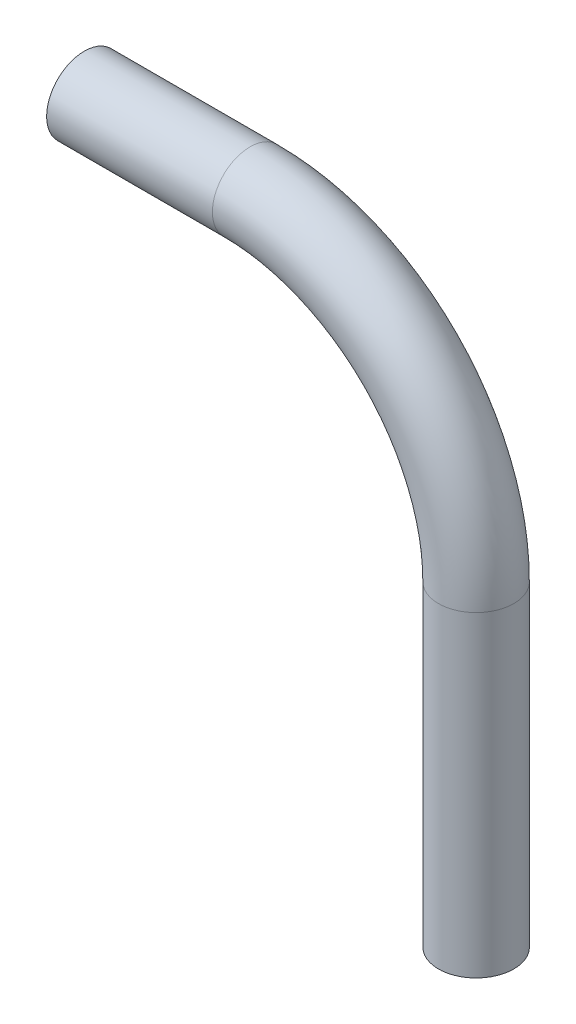
SolidWorks part; units mm, degrees
material "6061-T6 (SS)"
ref_plane "Front Plane" through (0, 0, 0) normal (0, 0, 1) x (1, 0, 0)
ref_plane "Top Plane" through (0, 0, 0) normal (0, 1, 0) x (1, 0, 0)
ref_plane "Right Plane" through (0, 0, 0) normal (1, 0, 0) x (0, 0, -1)
sketch "Sketch1" plane through (0, 0, 0) normal (0, 0, 1) x (1, 0, 0)
  line L0 (35.3114, 20.9627) -> (49.2814, 20.9627)
  line L1 (68.3314, 1.9127) -> (68.3314, -24.7573)
  line L2 (68.3314, -24.7573) -> (68.3314, 23.4845)
  line L3 (35.3114, 20.9627) -> (71.7681, 20.9627)
  arc A0 (49.2814, 20.9627) -> (68.3314, 1.9127) centre (49.2814, 1.9127) cw
  point P4 (68.3314, 20.9627)
  point P8 (0, 0)
  dimension "D1" = 19.05
  dimension "D2" = 33.02
  dimension "D3" = 45.72
  dimension "D4" = 90
ref_plane "Plane1" through (35.3114, 20.9627, 0) normal (1, 0, 0) x (0, 0, -1)
sketch "Sketch2" plane through (35.3114, 20.9627, 0) normal (1, 0, 0) x (0, 0, -1)
  line L0 (0, -45.72) -> (0, 2.5218) construction
  circle A0 centre (0, 0) radius 3.175
  circle A1 centre (0, 0) radius 1.524
  point P5 (0, 0)
  dimension "D1" = 6.35
  dimension "D2" = 3.048
sweep "Sweep1" add profiles "Sketch2" path "Sketch1"
